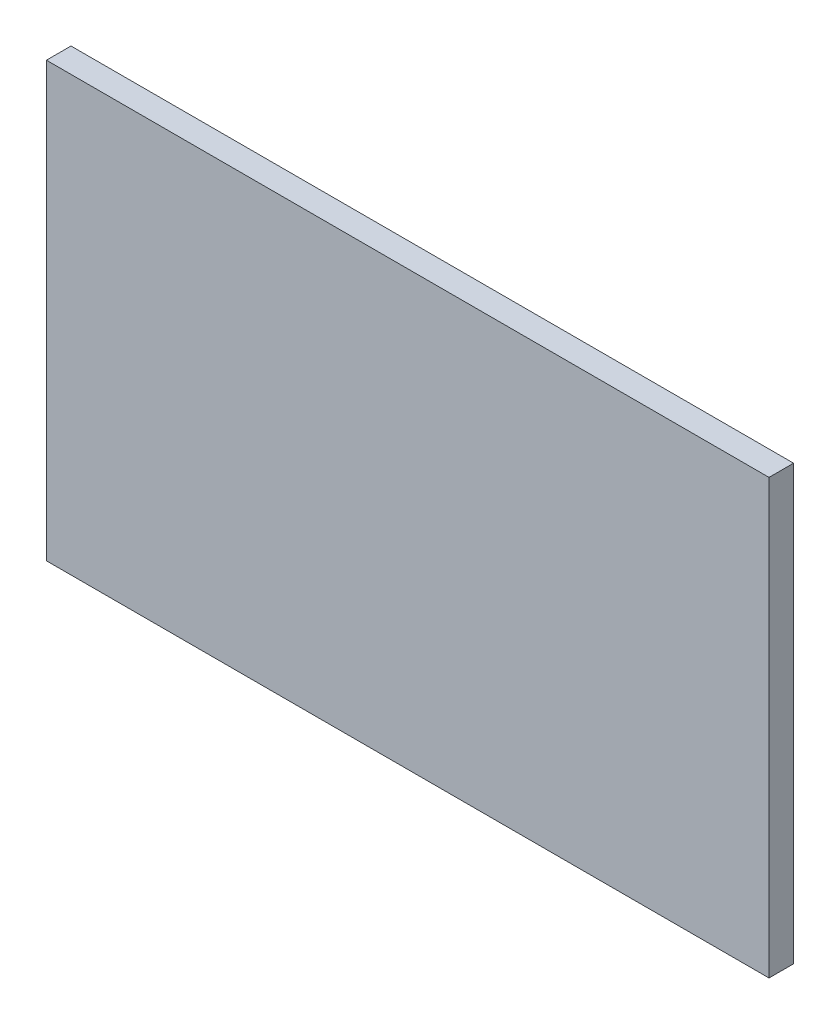
SolidWorks part; units mm, degrees
ref_plane "Front Plane" through (0, 0, 0) normal (0, 0, 1) x (1, 0, 0)
ref_plane "Top Plane" through (0, 0, 0) normal (0, 1, 0) x (1, 0, 0)
ref_plane "Right Plane" through (0, 0, 0) normal (1, 0, 0) x (0, 0, -1)
sketch "Sketch1" plane through (0, 0, 0) normal (0, 0, 1) x (1, 0, 0)
  line L1 (500, -300) -> (-500, -300)
  line L2 (500, -300) -> (500, 300)
  line L3 (500, 300) -> (-500, 300)
  line L4 (-500, -300) -> (-500, 300)
  line L5 (500, -300) -> (-500, 300) construction
  line L6 (500, 300) -> (-500, -300) construction
  point P0 (0, 0)
  dimension "D1" = 1000
  dimension "D2" = 600
extrude "Boss-Extrude1" add sketch "Sketch1" along normal blind 34
